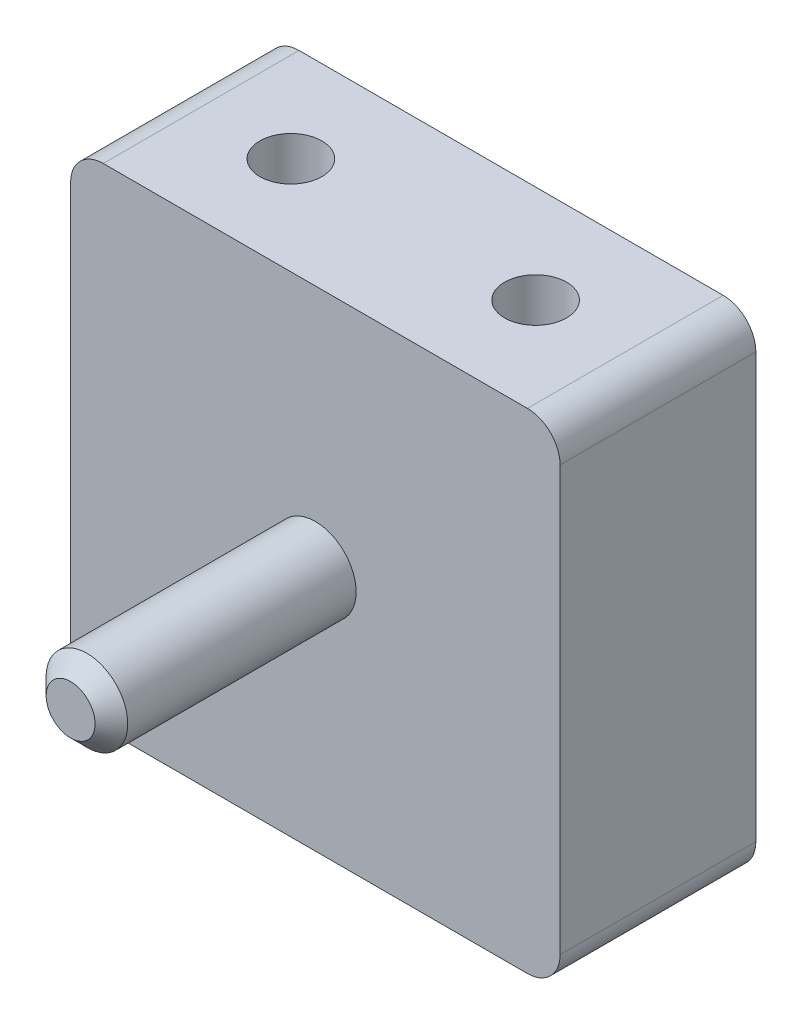
SolidWorks part; units mm, degrees
ref_plane "Front Plane" through (0, 0, 0) normal (0, 0, 1) x (1, 0, 0)
ref_plane "Top Plane" through (0, 0, 0) normal (0, 1, 0) x (1, 0, 0)
ref_plane "Right Plane" through (0, 0, 0) normal (1, 0, 0) x (0, 0, -1)
sketch "Sketch1" plane through (0, 0, 0) normal (0, 0, 1) x (1, 0, 0)
  line L1 (19.05, -19.05) -> (-19.05, -19.05)
  line L2 (19.05, -19.05) -> (19.05, 19.05)
  line L3 (19.05, 19.05) -> (-19.05, 19.05)
  line L4 (-19.05, -19.05) -> (-19.05, 19.05)
  line L5 (19.05, -19.05) -> (-19.05, 19.05) construction
  line L6 (19.05, 19.05) -> (-19.05, -19.05) construction
  circle A1 centre (0, 0) radius 1.5875
  point P0 (0, 0)
  dimension "D3" = 3.175
  dimension "D1" = 38.1
  dimension "D2" = 38.1
extrude "Boss-Extrude2" add sketch "Sketch1" along normal blind 15.24
sketch "Sketch3" plane through (0, 0, 15.24) normal (0, 0, 1) x (1, 0, 0)
  line L4 (-19.05, 19.05) -> (-19.05, -19.05)
  line L5 (-19.05, -19.05) -> (19.05, -19.05)
  line L6 (19.05, -19.05) -> (19.05, 19.05)
  line L7 (19.05, 19.05) -> (-19.05, 19.05)
  line L8 (-19.05, 19.05) -> (-19.05, -19.05)
  line L9 (-19.05, -19.05) -> (19.05, -19.05)
  line L10 (19.05, -19.05) -> (19.05, 19.05)
  line L11 (19.05, 19.05) -> (-19.05, 19.05)
  circle A0 centre (0, 0) radius 3.175
  dimension "D2" = 6.35
  dimension "D1" = 0
extrude "Boss-Extrude3" add sketch "Sketch3" along normal blind 19.05 contours A0
fillet "Fillet2" radius 2.54 4 edges at (-19.05, -19.05, 7.62) (19.05, -19.05, 7.62) (19.05, 19.05, 7.62) (-19.05, 19.05, 7.62)
chamfer "Chamfer1" distance 1.27 angle 45 1 edges at (3.175, 0, 34.29)
sketch "Sketch4" plane through (0, -19.05, 0) normal (0, -1, 0) x (1, 0, 0)
  line L0 (19.05, 15.24) -> (16.51, 15.24) construction
  line L1 (16.51, 0) -> (19.05, 0) construction
  line L2 (19.05, 0) -> (19.05, 15.24) construction
  line L3 (-16.51, 15.24) -> (-19.05, 15.24) construction
  line L4 (-19.05, 15.24) -> (-19.05, 0) construction
  line L5 (-19.05, 0) -> (-16.51, 0) construction
  line L6 (16.51, 15.24) -> (-16.51, 15.24) construction
  line L7 (-16.51, 0) -> (16.51, 0) construction
  line L8 (19.05, 15.24) -> (16.51, 15.24)
  line L9 (16.51, 0) -> (19.05, 0)
  line L10 (19.05, 0) -> (19.05, 15.24)
  line L11 (-16.51, 15.24) -> (-19.05, 15.24)
  line L12 (-19.05, 15.24) -> (-19.05, 0)
  line L13 (-19.05, 0) -> (-16.51, 0)
  line L14 (16.51, 15.24) -> (-16.51, 15.24)
  line L15 (-16.51, 0) -> (16.51, 0)
  line L16 (0, 15.24) -> (0, 0) construction
  line L17 (0, 7.62) -> (-9.525, 7.62) construction
  line L18 (0, 7.62) -> (9.525, 7.62) construction
  circle A0 centre (-9.525, 7.62) radius 2.413
  circle A1 centre (9.525, 7.62) radius 2.413
  dimension "D3" = 4.826
  dimension "D1" = 7.62
  dimension "D2" = 7.62
  dimension "D4" = 9.525
extrude "Cut-Extrude2" cut sketch "Sketch4" against normal blind 7.62 contours A0 | A1
sketch "Sketch5" plane through (0, 19.05, 0) normal (0, 1, 0) x (1, 0, 0)
  line L0 (-19.05, -15.24) -> (-16.51, -15.24) construction
  line L1 (-16.51, 0) -> (-19.05, 0) construction
  line L2 (-19.05, 0) -> (-19.05, -15.24) construction
  line L3 (16.51, -15.24) -> (19.05, -15.24) construction
  line L4 (19.05, -15.24) -> (19.05, 0) construction
  line L5 (19.05, 0) -> (16.51, 0) construction
  line L6 (-16.51, -15.24) -> (16.51, -15.24) construction
  line L7 (16.51, 0) -> (-16.51, 0) construction
  line L8 (-19.05, -15.24) -> (-16.51, -15.24)
  line L9 (-16.51, 0) -> (-19.05, 0)
  line L10 (-19.05, 0) -> (-19.05, -15.24)
  line L11 (16.51, -15.24) -> (19.05, -15.24)
  line L12 (19.05, -15.24) -> (19.05, 0)
  line L13 (19.05, 0) -> (16.51, 0)
  line L14 (-16.51, -15.24) -> (16.51, -15.24)
  line L15 (16.51, 0) -> (-16.51, 0)
  line L16 (0, 0) -> (0, -15.24) construction
  line L17 (0, -7.62) -> (-9.525, -7.62) construction
  line L18 (0, -7.62) -> (9.525, -7.62) construction
  circle A0 centre (9.525, -7.62) radius 2.413
  circle A1 centre (-9.525, -7.62) radius 2.413
  dimension "D5" = 4.826
  dimension "D1" = 7.62
  dimension "D2" = 7.62
  dimension "D3" = 9.525
extrude "Cut-Extrude3" cut sketch "Sketch5" against normal blind 7.62 contours A0 | A1
sketch "Sketch6" plane through (0, 19.05, 0) normal (0, 1, 0) x (1, 0, 0)
  circle A0 centre (9.525, -7.62) radius 2.413 construction
  circle A1 centre (-9.525, -7.62) radius 2.413 construction
  circle A2 centre (9.525, -7.62) radius 2.413
  circle A3 centre (-9.525, -7.62) radius 2.413
extrude "Cut-Extrude4" cut sketch "Sketch6" against normal through all
